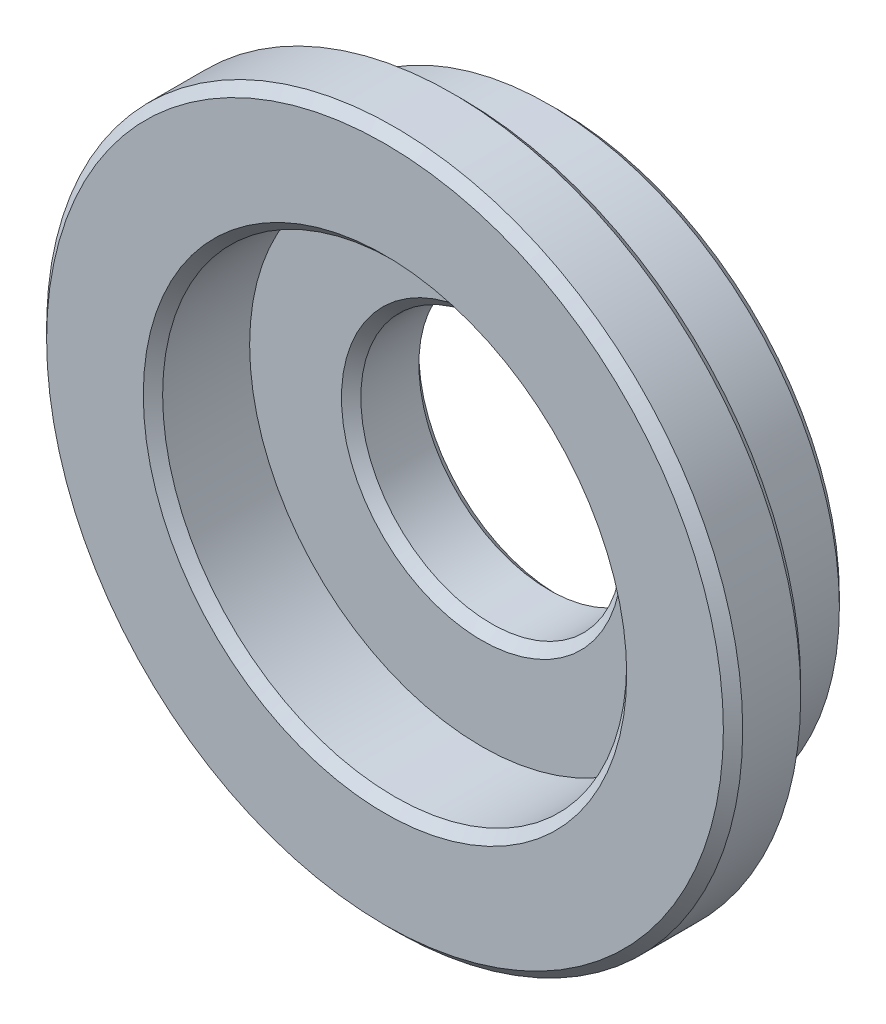
SolidWorks part; units mm, degrees
material "Aluminium"
ref_plane "Front Plane" through (0, 0, 0) normal (0, 0, 1) x (1, 0, 0)
ref_plane "Top Plane" through (0, 0, 0) normal (0, 1, 0) x (1, 0, 0)
ref_plane "Right Plane" through (0, 0, 0) normal (1, 0, 0) x (0, 0, -1)
sketch "Sketch1" plane through (0, 0, 0) normal (0, 1, 0) x (1, 0, 0)
  line L0 (2.5, -0.8) -> (3.5, -0.8)
  line L1 (3.5, -0.8) -> (3.6, -0.7)
  line L2 (3.6, -0.7) -> (3.6, -0.1)
  line L3 (3.6, -0.1) -> (3.5, 0)
  line L4 (3.5, 0) -> (3, 0)
  line L5 (3, 0) -> (3, 0.9)
  line L6 (3, 0.9) -> (2.9, 1)
  line L7 (2.9, 1) -> (1.45, 1)
  line L8 (1.45, 1) -> (1.35, 0.9)
  line L9 (1.35, 0.9) -> (1.35, 0.3)
  line L10 (1.35, 0.3) -> (1.45, 0.2)
  line L11 (1.45, 0.2) -> (2.4, 0.2)
  line L12 (2.4, 0.2) -> (2.4, -0.7)
  line L13 (2.4, -0.7) -> (2.5, -0.8)
  line L14 (0, 1) -> (0, -0.8) construction
revolve "Revolve1" add sketch "Sketch1" angle 360 about L14
